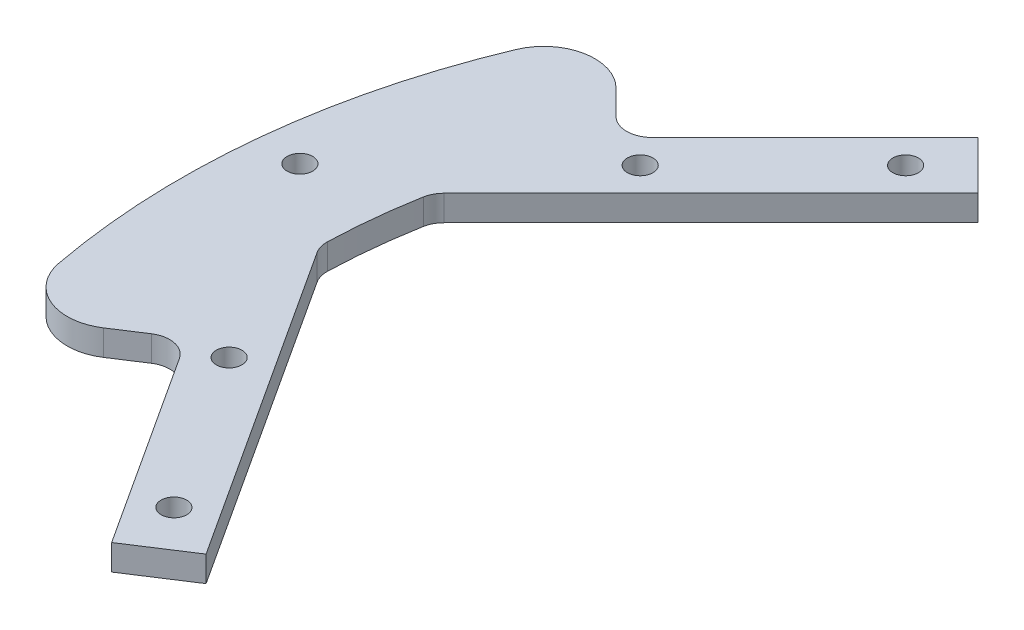
SolidWorks part; units mm, degrees
ref_plane "Front Plane" through (0, 0, 0) normal (0, 0, 1) x (1, 0, 0)
ref_plane "Top Plane" through (0, 0, 0) normal (0, 1, 0) x (1, 0, 0)
ref_plane "Right Plane" through (0, 0, 0) normal (1, 0, 0) x (0, 0, -1)
sketch "Sketch1" plane through (0, 0, 0) normal (0, 1, 0) x (1, 0, 0)
  line L0 (-74.629, 40.6879) -> (-63.6396, 29.6985)
  line L1 (-63.6396, 29.6985) -> (-42.4264, 50.9117)
  line L2 (-42.4264, 50.9117) -> (-36.7696, 45.2548)
  line L3 (-36.7696, 45.2548) -> (-68.725, 13.2994)
  line L5 (-69.9883, 1.28) -> (-45.3751, -36.6211)
  line L6 (-45.3751, -36.6211) -> (-52.0844, -40.9782)
  line L7 (-52.0844, -40.9782) -> (-68.4236, -15.8181)
  line L8 (-68.4236, -15.8181) -> (-81.4577, -24.2825)
  line L9 (0, 0) -> (-85, 0) construction
  line L10 (-43.8406, 43.8406) -> (0, 0) construction
  line L11 (-51.9976, -33.7676) -> (0, 0) construction
  arc A0 (-74.629, 40.6879) -> (-81.4577, -24.2825) centre (0, 0) ccw
  circle A1 centre (-43.8406, 43.8406) radius 1.5
  circle A2 centre (-59.397, 28.2843) radius 1.5
  circle A3 centre (-51.9976, -33.7676) radius 1.5
  circle A4 centre (-63.9796, -15.3169) radius 1.5
  arc A5 (-68.725, 13.2994) -> (-69.9883, 1.28) centre (0, 0) ccw
  dimension "D1" = 85
  dimension "D7" = 3
  dimension "D17" = 70
  dimension "D2" = 8
  dimension "D3" = 4
  dimension "D4" = 4
  dimension "D5" = 24
  dimension "D6" = 24
  dimension "D8" = 6
  dimension "D9" = 22
  dimension "D10" = 22
  dimension "D11" = 6
  dimension "D12" = 4
  dimension "D13" = 4
  dimension "D14" = 45
  dimension "D15" = 33
  dimension "D16" = 66
extrude "Boss-Extrude1" add sketch "Sketch1" along normal blind 3
fillet "Fillet1" radius 6 2 edges at (-74.629, 1.5, -40.6879) (-81.4577, 1.5, 24.2825)
fillet "Fillet2" radius 3 4 edges at (-69.9883, 1.5, -1.28) (-68.725, 1.5, -13.2994) (-63.6396, 1.5, -29.6985) (-68.4236, 1.5, 15.8181)
sketch "Sketch2" plane through (0, 3, 0) normal (0, 1, 0) x (1, 0, 0)
  circle A0 centre (-79.5, 8.5) radius 1.5
  dimension "D1" = 3
  dimension "D2" = 79.5
  dimension "D3" = 8.5
extrude "Cut-Extrude1" cut sketch "Sketch2" against normal up to next
